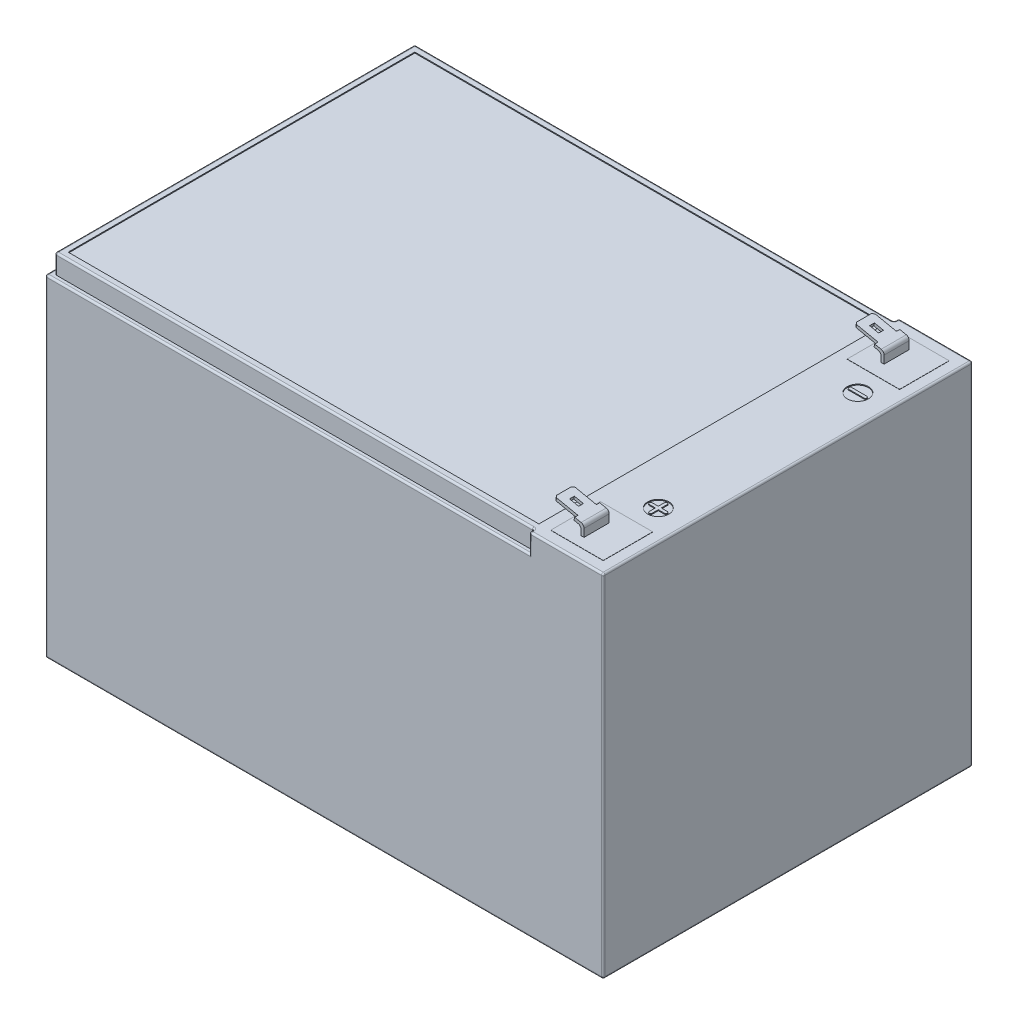
SolidWorks part; units mm, degrees
ref_plane "Front Plane" through (0, 0, 0) normal (0, 0, 1) x (1, 0, 0)
ref_plane "Top Plane" through (0, 0, 0) normal (0, 1, 0) x (1, 0, 0)
ref_plane "Right Plane" through (0, 0, 0) normal (1, 0, 0) x (0, 0, -1)
sketch "Sketch1" plane through (0, 0, 0) normal (0, 1, 0) x (1, 0, 0)
  line L1 (-75.0564, 43.5611) -> (75.9436, 43.5611)
  line L2 (-75.0564, 43.5611) -> (-75.0564, -56.4389)
  line L3 (-75.0564, -56.4389) -> (75.9436, -56.4389)
  line L4 (75.9436, 43.5611) -> (75.9436, -56.4389)
  dimension "D1" = 151
  dimension "D2" = 100
extrude "Boss-Extrude1" add sketch "Sketch1" along normal blind 95
ref_plane "Plane1" through (0, 0, 50.4389) normal (0, 0, 1) x (1, 0, 0)
sketch "Sketch2" plane through (0, 0, 50.4389) normal (0, 0, 1) x (1, 0, 0)
  line L0 (63.9436, 95) -> (63.9436, 97.3257)
  line L1 (-75.0564, 95) -> (75.9436, 95) construction
  line L2 (63.9436, 97.3257) -> (55.7698, 99.03)
  line L3 (55.7698, 99.03) -> (55.9331, 99.8131)
  line L4 (55.9331, 99.8131) -> (64.7436, 97.9761)
  line L5 (64.7436, 97.9761) -> (64.7436, 95)
  line L6 (64.7436, 95) -> (63.9436, 95)
  line L7 (75.9436, 95) -> (75.9436, 0) construction
  dimension "D1" = 12
  dimension "D2" = 9
  dimension "D3" = 0.8
  dimension "D4" = 0.8
extrude "Boss-Extrude2" add sketch "Sketch2" against normal blind 6.8
ref_plane "Plane2" through (0, 0, 6.4389) normal (0, 0, 1) x (1, 0, 0)
sketch "Sketch4" plane through (22.274, 106.8309, 0) normal (0.2041, 0.9789, 0) x (0.9789, -0.2041, 0)
  line L0 (40.7829, -43.6389) -> (40.7829, -44.5389)
  line L1 (43.3829, -43.6389) -> (34.3829, -43.6389) construction
  line L2 (40.7829, -44.5389) -> (34.3829, -44.5389)
  line L3 (34.3829, -43.6389) -> (34.3829, -50.4389) construction
  line L4 (34.3829, -44.5389) -> (34.3829, -43.6389)
  line L5 (34.3829, -43.6389) -> (40.7829, -43.6389)
  line L6 (40.7829, -49.5389) -> (40.7829, -50.4389)
  line L7 (-51.7, -50.4389) -> (51.7, -50.4389) construction
  line L8 (40.7829, -49.5389) -> (34.3829, -49.5389)
  line L9 (34.3829, -49.5389) -> (34.3829, -50.4389)
  line L10 (34.3829, -50.4389) -> (40.7829, -50.4389)
  line L12 (36.5829, -46.3889) -> (39.0829, -46.3889)
  line L13 (36.5829, -46.3889) -> (36.5829, -47.6889)
  line L14 (36.5829, -47.6889) -> (39.0829, -47.6889)
  line L15 (39.0829, -46.3889) -> (39.0829, -47.6889)
  dimension "D1" = 0.9
  dimension "D2" = 0.9
  dimension "D3" = 6.4
  dimension "D4" = 2.2
  dimension "D5" = 2.5
  dimension "D6" = 1.3
  dimension "D7" = 1.85
  dimension "D8" = 1.85
extrude "Cut-Extrude1" cut sketch "Sketch4" against normal up to next (0.8 mm away)
chamfer "Chamfer1" distance 0.5 angle 45 2 edges at (55.8514, 99.4215, 44.5389) (55.8514, 99.4215, 49.5389)
fillet "Fillet1" radius 1 2 edges at (63.9436, 97.3257, 47.0389) (64.7436, 97.9761, 47.0389)
mirror "Mirror1" about plane through (0, 0, 6.4389) normal (0, 0, 1) of "Fillet1", "Chamfer1", "Cut-Extrude1", "Boss-Extrude2"
sketch "Sketch5" plane through (0, 95, 0) normal (0, 1, 0) x (1, 0, 0)
  line L0 (55.9436, -56.4389) -> (55.9436, -55.1389)
  line L1 (-75.0564, -56.4389) -> (75.9436, -56.4389) construction
  line L2 (55.9436, -55.1389) -> (-73.7564, -55.1389)
  line L3 (-73.7564, -55.1389) -> (-73.7564, 42.2611)
  line L4 (-73.7564, 42.2611) -> (55.9436, 42.2611)
  line L5 (55.9436, 42.2611) -> (55.9436, 43.5611)
  line L6 (75.9436, 43.5611) -> (-75.0564, 43.5611) construction
  line L7 (55.9436, 43.5611) -> (-75.0564, 43.5611)
  line L8 (-75.0564, 43.5611) -> (-75.0564, -56.4389)
  line L9 (-75.0564, -56.4389) -> (55.9436, -56.4389)
  line L10 (75.9436, -56.4389) -> (75.9436, 43.5611) construction
  dimension "D1" = 1.3
  dimension "D2" = 1.3
  dimension "D3" = 1.3
  dimension "D4" = 20
  dimension "D5" = 20
extrude "Cut-Extrude2" cut sketch "Sketch5" against normal blind 5.2
fillet "Fillet2" radius 0.5 25 edges at (0.4436, 0, -43.5611) (-75.0564, 44.9, -43.5611) (-75.0564, 0, 6.4389) (-75.0564, 44.9, 56.4389) (75.9436, 0, 6.4389) (0.4436, 0, 56.4389) (75.9436, 47.5, -43.5611) (65.9436, 95, -43.5611) (55.9436, 92.4, -43.5611) (55.9436, 92.4, -42.2611) (55.9436, 95, -42.9111) (-9.5564, 89.8, -43.5611) (-8.9064, 95, -42.2611) (-73.7564, 92.4, -42.2611) (-73.7564, 92.4, 55.1389) (-75.0564, 89.8, 6.4389) (55.9436, 92.4, 55.1389) (-9.5564, 89.8, 56.4389) (55.9436, 92.4, 56.4389) (75.9436, 47.5, 56.4389) (75.9436, 95, 6.4389) (65.9436, 95, 56.4389) (55.9436, 95, 55.7889) (-8.9064, 95, 55.1389) (-73.7564, 95, 6.4389)
sketch "Sketch6" plane through (0, 95, 0) normal (0, 1, 0) x (1, 0, 0)
  line L0 (-73.7564, -54.6389) -> (-73.7564, 41.7611) construction
  line L1 (-71.9564, 40.4611) -> (55.4436, 40.4611)
  line L2 (-71.9564, 40.4611) -> (-71.9564, -53.3389)
  line L3 (-71.9564, -53.3389) -> (55.4436, -53.3389)
  line L4 (55.4436, 40.4611) -> (55.4436, -53.3389)
  line L5 (-73.2564, 42.2611) -> (55.4436, 42.2611) construction
  line L6 (55.4436, -55.1389) -> (-73.2564, -55.1389) construction
  line L7 (75.9436, 43.0611) -> (75.9436, -55.9389) construction
  line L8 (56.4436, 43.5611) -> (75.4436, 43.5611) construction
  line L9 (75.4436, -56.4389) -> (56.4436, -56.4389) construction
  line L10 (67.4436, -31.2889) -> (67.4436, -33.0389)
  line L11 (65.6936, 20.9611) -> (69.9936, 20.9611)
  line L12 (65.4436, 20.7111) -> (65.4436, 20.4111)
  line L13 (65.6936, 20.1611) -> (69.9936, 20.1611)
  line L14 (70.2436, 20.7111) -> (70.2436, 20.4111)
  line L15 (67.4436, -33.0389) -> (65.6936, -33.0389)
  line L16 (65.4436, -33.2889) -> (65.4436, -33.5889)
  line L17 (65.6936, -33.8389) -> (67.4436, -33.8389)
  line L18 (67.4436, -33.8389) -> (67.4436, -35.5889)
  line L19 (67.6936, -35.8389) -> (67.9936, -35.8389)
  line L20 (68.2436, -35.5889) -> (68.2436, -33.8389)
  line L21 (68.2436, -33.8389) -> (69.9936, -33.8389)
  line L22 (70.2436, -33.5889) -> (70.2436, -33.2889)
  line L23 (69.9936, -33.0389) -> (68.2436, -33.0389)
  line L24 (68.2436, -33.0389) -> (68.2436, -31.2889)
  line L25 (67.9936, -31.0389) -> (67.6936, -31.0389)
  line L27 (72.7436, 40.3611) -> (58.5436, 40.3611)
  line L28 (72.7436, 40.3611) -> (72.7436, 26.9611)
  line L29 (72.7436, 26.9611) -> (58.5436, 26.9611)
  line L30 (58.5436, 40.3611) -> (58.5436, 26.9611)
  line L31 (72.7436, -53.2389) -> (58.5436, -53.2389)
  line L32 (72.7436, -53.2389) -> (72.7436, -39.8389)
  line L33 (72.7436, -39.8389) -> (58.5436, -39.8389)
  line L34 (58.5436, -53.2389) -> (58.5436, -39.8389)
  circle A0 centre (67.8436, 20.5611) radius 2.875
  circle A1 centre (67.8436, -33.4389) radius 2.875
  arc A2 (69.9936, 20.1611) -> (70.2436, 20.4111) centre (69.9936, 20.4111) ccw
  arc A3 (70.2436, 20.7111) -> (69.9936, 20.9611) centre (69.9936, 20.7111) ccw
  arc A4 (65.6936, 20.1611) -> (65.4436, 20.4111) centre (65.6936, 20.4111) cw
  arc A5 (65.6936, 20.9611) -> (65.4436, 20.7111) centre (65.6936, 20.7111) ccw
  arc A6 (65.6936, -33.8389) -> (65.4436, -33.5889) centre (65.6936, -33.5889) cw
  arc A7 (65.4436, -33.2889) -> (65.6936, -33.0389) centre (65.6936, -33.2889) cw
  arc A8 (67.6936, -35.8389) -> (67.4436, -35.5889) centre (67.6936, -35.5889) cw
  arc A9 (67.9936, -35.8389) -> (68.2436, -35.5889) centre (67.9936, -35.5889) ccw
  arc A10 (69.9936, -33.8389) -> (70.2436, -33.5889) centre (69.9936, -33.5889) ccw
  arc A11 (70.2436, -33.2889) -> (69.9936, -33.0389) centre (69.9936, -33.2889) ccw
  arc A12 (68.2436, -31.2889) -> (67.9936, -31.0389) centre (67.9936, -31.2889) ccw
  arc A13 (67.6936, -31.0389) -> (67.4436, -31.2889) centre (67.6936, -31.2889) ccw
  dimension "D5" = 5.75
  dimension "D8" = 5.75
  dimension "D27" = 0.25
  dimension "D1" = 1.8
  dimension "D2" = 1.8
  dimension "D3" = 1.8
  dimension "D4" = 20.5
  dimension "D6" = 8.1
  dimension "D7" = 23
  dimension "D9" = 8.1
  dimension "D10" = 23
  dimension "D11" = 0.4
  dimension "D12" = 0.4
  dimension "D13" = 2.4
  dimension "D14" = 2.4
  dimension "D15" = 0.4
  dimension "D16" = 0.4
  dimension "D17" = 0.4
  dimension "D18" = 0.4
  dimension "D19" = 0.4
  dimension "D20" = 0.4
  dimension "D21" = 0.4
  dimension "D22" = 0.4
  dimension "D23" = 2.4
  dimension "D24" = 2.4
  dimension "D25" = 2.4
  dimension "D26" = 2.4
  dimension "D28" = 3.2
  dimension "D29" = 3.2
  dimension "D30" = 14.2
  dimension "D31" = 13.4
  dimension "D32" = 3.2
  dimension "D33" = 3.2
  dimension "D34" = 14.2
  dimension "D35" = 13.4
extrude "Cut-Extrude3" cut sketch "Sketch6" against normal blind 0.25
sketch "Sketch7" plane through (0, 94.75, 0) normal (0, 1, 0) x (1, 0, 0)
  line L0 (58.5436, 26.9611) -> (72.7436, 26.9611) construction
  line L1 (72.7436, 26.9611) -> (72.7436, 40.3611) construction
  line L2 (58.5436, 40.3611) -> (58.5436, 26.9611) construction
  line L3 (72.7436, 40.3611) -> (58.5436, 40.3611) construction
  line L4 (58.5436, 26.9611) -> (72.7436, 26.9611)
  line L5 (72.7436, 26.9611) -> (72.7436, 40.3611)
  line L6 (58.5436, 40.3611) -> (58.5436, 26.9611)
  line L7 (72.7436, 40.3611) -> (58.5436, 40.3611)
extrude "Boss-Extrude3" add sketch "Sketch7" along normal blind 0.3
sketch "Sketch8" plane through (0, 94.75, 0) normal (0, 1, 0) x (1, 0, 0)
  line L0 (58.5436, -53.2389) -> (72.7436, -53.2389) construction
  line L1 (72.7436, -53.2389) -> (72.7436, -39.8389) construction
  line L2 (58.5436, -39.8389) -> (58.5436, -53.2389) construction
  line L3 (72.7436, -39.8389) -> (58.5436, -39.8389) construction
  line L4 (58.5436, -53.2389) -> (72.7436, -53.2389)
  line L5 (72.7436, -53.2389) -> (72.7436, -39.8389)
  line L6 (58.5436, -39.8389) -> (58.5436, -53.2389)
  line L7 (72.7436, -39.8389) -> (58.5436, -39.8389)
extrude "Boss-Extrude4" add sketch "Sketch8" along normal blind 0.3
ref_plane "Plane3" through (0.4436, 0, 0) normal (-1, 0, 0) x (0, 0, 1)
sketch "Sketch9" plane through (0, 0, 0) normal (0, -1, 0) x (1, 0, 0)
  line L0 (-70.0564, 43.7389) -> (-70.0564, 50.9389)
  line L1 (-69.5564, 51.4389) -> (-62.3564, 51.4389)
  line L2 (-61.8564, 50.9389) -> (-61.8564, 49.9389)
  line L3 (-62.3564, 49.4389) -> (-68.0564, 49.4389)
  line L4 (-68.0564, 49.4389) -> (-68.0564, 43.7389)
  line L5 (-68.5564, 43.2389) -> (-69.5564, 43.2389)
  line L6 (-74.5564, 56.4389) -> (75.4436, 56.4389) construction
  line L7 (-75.0564, -43.0611) -> (-75.0564, 55.9389) construction
  arc A0 (-68.5564, 43.2389) -> (-68.0564, 43.7389) centre (-68.5564, 43.7389) ccw
  arc A1 (-69.5564, 43.2389) -> (-70.0564, 43.7389) centre (-69.5564, 43.7389) cw
  arc A2 (-62.3564, 49.4389) -> (-61.8564, 49.9389) centre (-62.3564, 49.9389) ccw
  arc A3 (-61.8564, 50.9389) -> (-62.3564, 51.4389) centre (-62.3564, 50.9389) ccw
  arc A4 (-69.5564, 51.4389) -> (-70.0564, 50.9389) centre (-69.5564, 50.9389) ccw
  dimension "D7" = 0.5
  dimension "D1" = 8.2
  dimension "D2" = 8.2
  dimension "D3" = 2
  dimension "D4" = 2
  dimension "D5" = 5
  dimension "D6" = 5
extrude "Boss-Extrude5" add sketch "Sketch9" along normal blind 0.5
mirror "Mirror2" about plane through (0.4436, 0, 0) normal (-1, 0, 0) of "Boss-Extrude5"
mirror "Mirror3" about plane through (0, 0, 6.4389) normal (0, 0, 1) of "Mirror2", "Boss-Extrude5"
